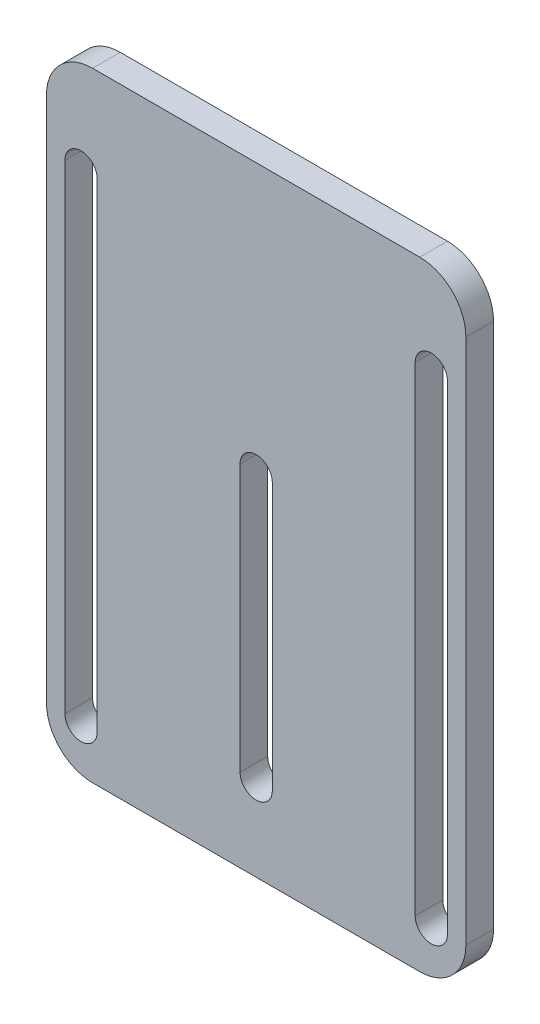
SolidWorks part; units mm, degrees
ref_plane "Front Plane" through (0, 0, 0) normal (0, 0, 1) x (1, 0, 0)
ref_plane "Top Plane" through (0, 0, 0) normal (0, 1, 0) x (1, 0, 0)
ref_plane "Right Plane" through (0, 0, 0) normal (1, 0, 0) x (0, 0, -1)
sketch "Sketch1" plane through (0, 0, 0) normal (0, 0, 1) x (1, 0, 0)
  line L0 (-38, 46.8736) -> (-38, -57.1362) construction
  line L1 (-35.5, -67.1362) -> (35.5, -67.1362)
  line L2 (-45.5, -57.1362) -> (-45.5, 57.1362)
  line L3 (-35.5, 67.1362) -> (35.5, 67.1362)
  line L4 (45.5, -57.1362) -> (45.5, 57.1362)
  line L5 (-45.5, -67.1362) -> (45.5, 67.1362) construction
  line L6 (-45.5, 67.1362) -> (45.5, -67.1362) construction
  line L7 (-34.5, 46.8736) -> (-34.5, -57.1362)
  line L8 (-41.5, 46.8736) -> (-41.5, -57.1362)
  line L9 (38, -57.1362) -> (38, 46.8736) construction
  line L10 (34.5, -57.1362) -> (34.5, 46.8736)
  line L11 (41.5, -57.1362) -> (41.5, 46.8736)
  line L12 (-38, -5.1313) -> (38, -5.1313) construction
  line L13 (0, 8.7916) -> (0, -49.1362) construction
  line L14 (3.5, 8.7916) -> (3.5, -49.1362)
  line L15 (-3.5, 8.7916) -> (-3.5, -49.1362)
  arc A0 (-34.5, 46.8736) -> (-41.5, 46.8736) centre (-38, 46.8736) ccw
  arc A1 (-41.5, -57.1362) -> (-34.5, -57.1362) centre (-38, -57.1362) ccw
  arc A2 (34.5, -57.1362) -> (41.5, -57.1362) centre (38, -57.1362) ccw
  arc A3 (41.5, 46.8736) -> (34.5, 46.8736) centre (38, 46.8736) ccw
  arc A4 (3.5, 8.7916) -> (-3.5, 8.7916) centre (0, 8.7916) ccw
  arc A5 (-3.5, -49.1362) -> (3.5, -49.1362) centre (0, -49.1362) ccw
  arc A6 (-45.5, 57.1362) -> (-35.5, 67.1362) centre (-35.5, 57.1362) cw
  arc A7 (35.5, 67.1362) -> (45.5, 57.1362) centre (35.5, 57.1362) cw
  arc A8 (35.5, -67.1362) -> (45.5, -57.1362) centre (35.5, -57.1362) ccw
  arc A9 (-35.5, -67.1362) -> (-45.5, -57.1362) centre (-35.5, -57.1362) cw
  point P0 (0, 0)
  point P8 (-38, -5.1313)
  point P13 (38, -5.1313)
  point P20 (0, -5.1313)
  point P21 (0, -20.1723)
  point P30 (0, -7.4577)
  point P43 (-41.5, 46.7063)
  point P44 (0, 19.2624)
  point P45 (38, 56.1825)
  point P46 (0, -36.313)
  point P47 (38, 48.5227)
  point P48 (0, 12.5485)
  point P49 (38, 46.5862)
  point P50 (0, 8.7916)
  point P51 (38, 46.8736)
  dimension "D3" = 10
  dimension "D1" = 7
  dimension "D2" = 69
  dimension "D4" = 4
  dimension "D5" = 8
  dimension "D6" = 10
extrude "Boss-Extrude1" add sketch "Sketch1" along normal blind 6
